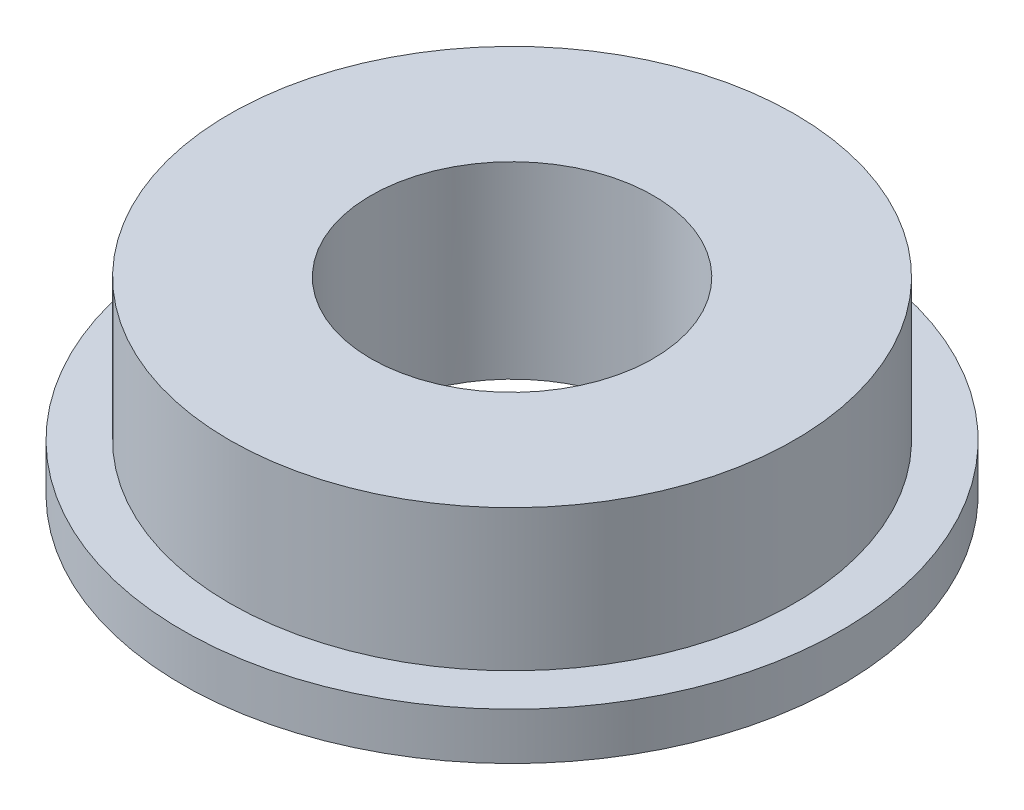
SolidWorks part; units mm, degrees
ref_plane "前视基准面" through (0, 0, 0) normal (0, 0, 1) x (1, 0, 0)
ref_plane "上视基准面" through (0, 0, 0) normal (0, 1, 0) x (1, 0, 0)
ref_plane "右视基准面" through (0, 0, 0) normal (1, 0, 0) x (0, 0, -1)
sketch "草图1" plane through (0, 0, 0) normal (0, 0, 1) x (1, 0, 0)
  line L0 (0, 0) -> (6, 0)
  line L1 (6, 0) -> (6, -3)
  line L2 (6, -3) -> (7, -3)
  line L3 (7, -3) -> (7, -4)
  line L4 (7, -4) -> (0, -4)
  line L5 (0, -4) -> (0, 0)
  dimension "D1" = 6
  dimension "D2" = 4
  dimension "D3" = 3
  dimension "D4" = 1
revolve "旋转1" add sketch "草图1" angle 360 about L5
sketch "草图2" plane through (0, 0, 0) normal (0, 1, 0) x (1, 0, 0)
  circle A0 centre (0, 0) radius 3
  dimension "D1" = 6
extrude "切除-拉伸1" cut sketch "草图2" against normal up to surface (4 mm away) up to face at (0, -4, -7)
